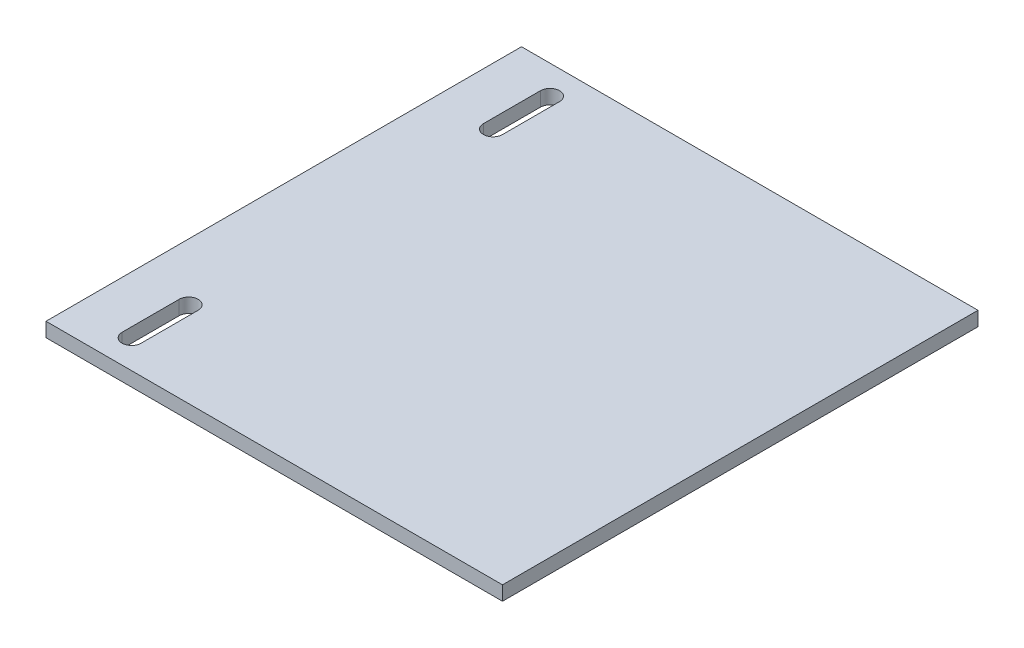
SolidWorks part; units mm, degrees
material "ASTM A36 Steel"
ref_plane "Front Plane" through (0, 0, 0) normal (0, 0, 1) x (1, 0, 0)
ref_plane "Top Plane" through (0, 0, 0) normal (0, 1, 0) x (1, 0, 0)
ref_plane "Right Plane" through (0, 0, 0) normal (1, 0, 0) x (0, 0, -1)
sketch "Sketch1" plane through (0, 0, 0) normal (0, 1, 0) x (1, 0, 0)
  line L1 (76.2, 79.375) -> (-76.2, 79.375)
  line L2 (76.2, 79.375) -> (76.2, -79.375)
  line L3 (76.2, -79.375) -> (-76.2, -79.375)
  line L4 (-76.2, 79.375) -> (-76.2, -79.375)
  line L5 (76.2, 79.375) -> (-76.2, -79.375) construction
  line L6 (76.2, -79.375) -> (-76.2, 79.375) construction
  point P0 (0, 0)
  dimension "D1" = 158.75
  dimension "D2" = 152.4
extrude "Boss-Extrude1" add sketch "Sketch1" along normal blind 4.7625
sketch "Sketch2" plane through (0, 4.7625, 0) normal (0, 1, 0) x (1, 0, 0)
  line L0 (-76.2, 79.375) -> (-76.2, -79.375) construction
  line L3 (57.15, -60.325) -> (-57.15, -60.325) construction
  line L6 (57.15, -60.325) -> (57.15, 60.325) construction
  line L7 (57.15, 60.325) -> (-57.15, 60.325) construction
  line L8 (-57.15, -60.325) -> (-57.15, 60.325) construction
  line L9 (57.15, -60.325) -> (-57.15, 60.325) construction
  line L10 (57.15, 60.325) -> (-57.15, -60.325) construction
  line L11 (-76.2, -79.375) -> (76.2, -79.375) construction
  line L12 (-57.15, -50.8) -> (-57.15, -69.85) construction
  line L13 (-53.975, -50.8) -> (-53.975, -69.85)
  line L14 (-60.325, -50.8) -> (-60.325, -69.85)
  line L15 (-57.15, 50.8) -> (-57.15, 69.85) construction
  line L16 (-60.325, 50.8) -> (-60.325, 69.85)
  line L17 (-53.975, 50.8) -> (-53.975, 69.85)
  line L18 (57.15, -50.8) -> (57.15, -69.85) construction
  line L19 (60.325, -50.8) -> (60.325, -69.85)
  line L20 (53.975, -50.8) -> (53.975, -69.85)
  line L21 (57.15, 69.85) -> (57.15, 50.8) construction
  line L22 (60.325, 69.85) -> (60.325, 50.8)
  line L23 (53.975, 69.85) -> (53.975, 50.8)
  arc A0 (-53.975, -50.8) -> (-60.325, -50.8) centre (-57.15, -50.8) ccw
  arc A1 (-60.325, -69.85) -> (-53.975, -69.85) centre (-57.15, -69.85) ccw
  arc A2 (-60.325, 50.8) -> (-53.975, 50.8) centre (-57.15, 50.8) ccw
  arc A3 (-53.975, 69.85) -> (-60.325, 69.85) centre (-57.15, 69.85) ccw
  arc A4 (60.325, -50.8) -> (53.975, -50.8) centre (57.15, -50.8) ccw
  arc A5 (53.975, -69.85) -> (60.325, -69.85) centre (57.15, -69.85) ccw
  arc A6 (60.325, 69.85) -> (53.975, 69.85) centre (57.15, 69.85) ccw
  arc A7 (53.975, 50.8) -> (60.325, 50.8) centre (57.15, 50.8) ccw
  point P0 (0, 0)
  point P11 (-57.15, -60.325)
  point P18 (-57.15, 60.325)
  point P27 (57.15, -60.325)
  point P34 (57.15, 60.325)
  dimension "D1" = 19.05
  dimension "D2" = 19.05
  dimension "D3" = 19.05
  dimension "D4" = 6.35
extrude "Cut-Extrude1" cut sketch "Sketch2" against normal through all contours L17 A3 L16 A2 | L14 A1 L13 A0
